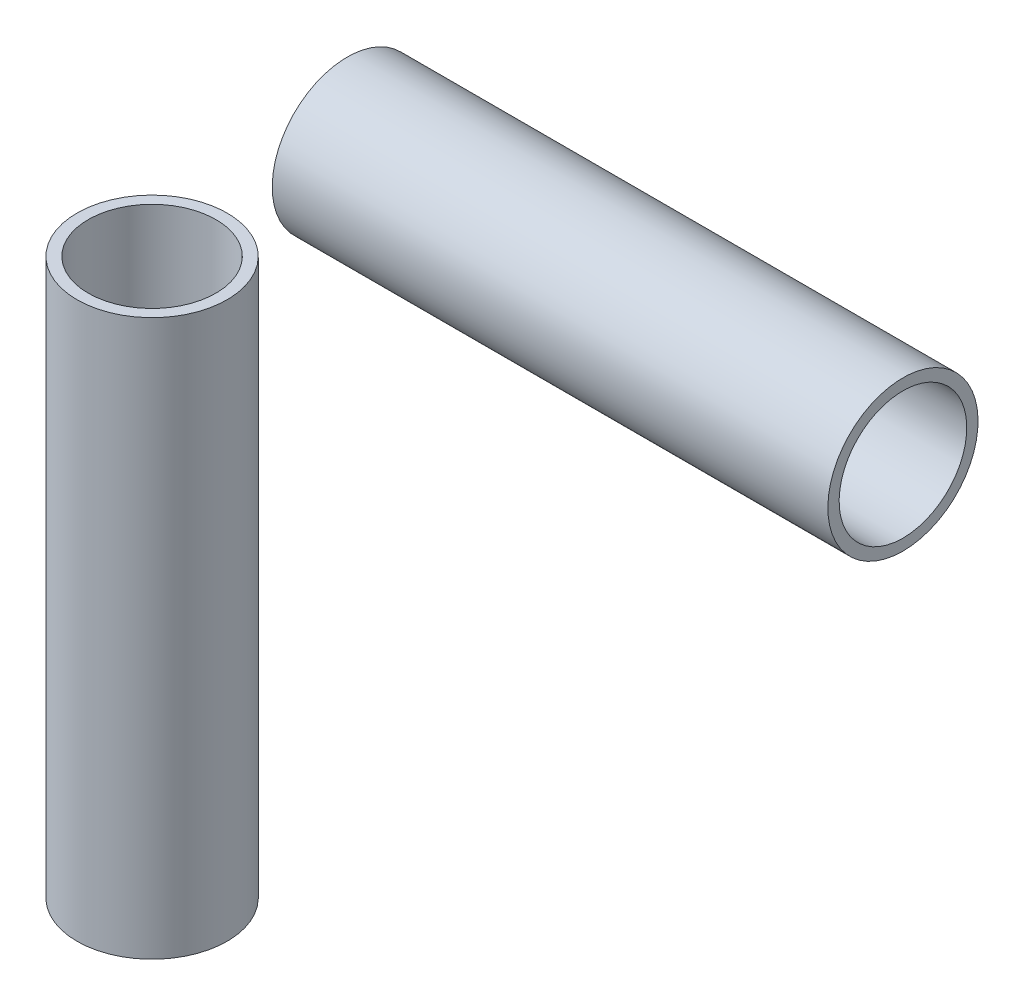
SolidWorks part; units mm, degrees
material "304L_(1.4307)"
ref_plane "Plan de face" through (0, 0, 0) normal (0, 0, 1) x (1, 0, 0)
ref_plane "Plan de dessus" through (0, 0, 0) normal (0, 1, 0) x (1, 0, 0)
ref_plane "Plan de droite" through (0, 0, 0) normal (1, 0, 0) x (0, 0, -1)
sketch3d "Esquisse3D1"
  line L0 (0, 0, 0) -> (0, 74, 0)
  line L1 (26, 100, 0) -> (100, 100, 0)
  arc A0 (0, 74, 0) -> (26, 100, 0) centre (26, 74, 0) ccw construction
  point P6 (0, 100, 0)
  point P7 (26, 74, -26)
  dimension "D3" = 26
  dimension "D1" = 100
other "Tubes metriques roulés soudés TUBE Ø 0020 X 1,5 MM(1)"
ref_plane "Plan1" through (0, 0, 0) normal (0, 1, 0) x (1, 0, 0)
sketch "Tube Metrique roulé-soudé" plane through (0, 0, 0) normal (0, 1, 0) x (1, 0, 0)
  circle A0 centre (0, 0) radius 10
  circle A1 centre (0, 0) radius 8.5
  point P3 (0, 10)
  point P5 (-10, 0)
  point P6 (10, 0)
  point P7 (0, -10)
  point P8 (0, 0)
  point P9 (0, 0)
  dimension "Diametre-exterieur" = 20
  dimension "Epaisseur" = 1.5
